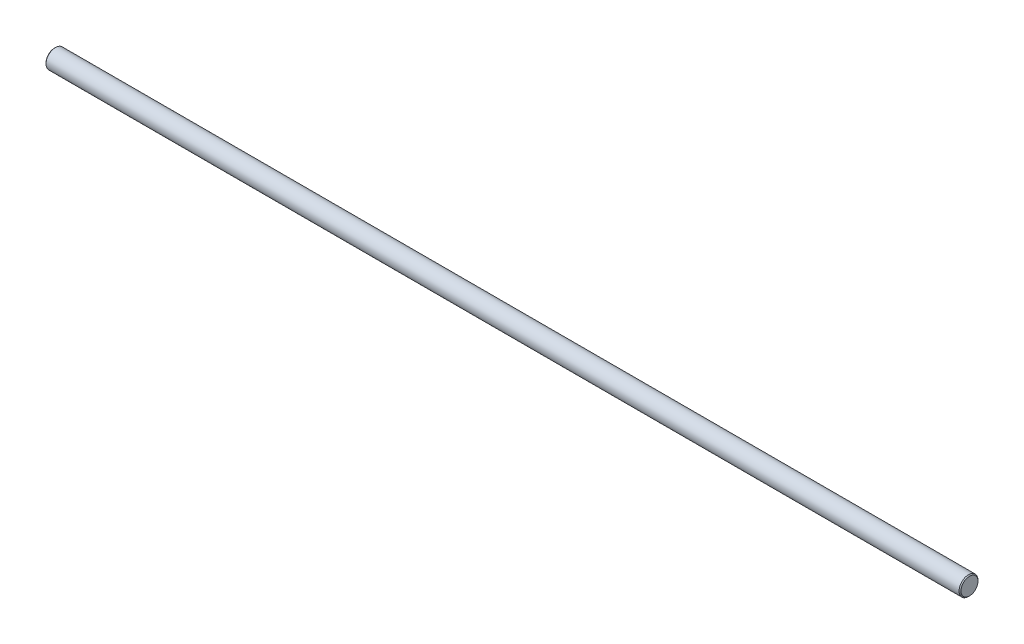
SolidWorks part; units mm, degrees
ref_plane "Front Plane" through (0, 0, 0) normal (0, 0, 1) x (1, 0, 0)
ref_plane "Top Plane" through (0, 0, 0) normal (0, 1, 0) x (1, 0, 0)
ref_plane "Right Plane" through (0, 0, 0) normal (1, 0, 0) x (0, 0, -1)
ref_plane "Plane1" through (0, 0, 0) normal (0, 0, 1) x (1, 0, 0)
sketch "Sketch1" plane through (0, 0, 0) normal (0, 0, 1) x (1, 0, 0)
  line L0 (0, 0) -> (0, 4.5)
  line L1 (0, 4.5) -> (0.5, 5)
  line L2 (0.5, 5) -> (482.5, 5)
  line L3 (482.5, 5) -> (483, 4.5)
  line L4 (483, 4.5) -> (483, 0)
  line L5 (483, 0) -> (0, 0)
  line L6 (483, 0) -> (0, 0) construction
  dimension "D1" = 483
  dimension "D2" = 135
  dimension "D3" = 135
  dimension "D4" = 5
  dimension "D5" = 0.5
  dimension "D6" = 0.5
revolve "Revolve1" add sketch "Sketch1" angle 360 about L6
ref_plane "Plane2" through (241.5, 0, 0) normal (-1, 0, 0) x (0, 0, 1)
